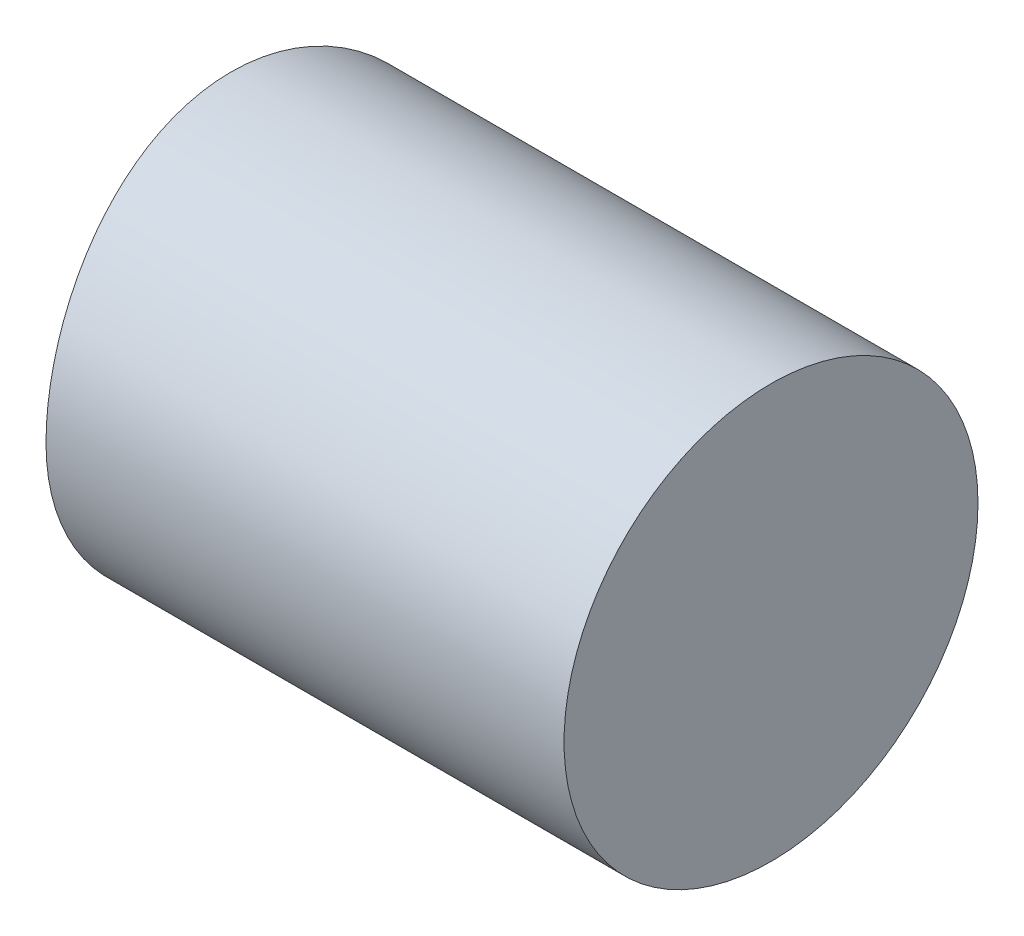
SolidWorks part; units mm, degrees
ref_plane "Front Plane" through (0, 0, 0) normal (0, 0, 1) x (1, 0, 0)
ref_plane "Top Plane" through (0, 0, 0) normal (0, 1, 0) x (1, 0, 0)
ref_plane "Right Plane" through (0, 0, 0) normal (1, 0, 0) x (0, 0, -1)
sketch "Sketch3" plane through (0, 0, 0) normal (1, 0, 0) x (0, 0, -1)
  circle A0 centre (0, 0) radius 2.921
  dimension "D1" = 5.842
extrude "Boss-Extrude2" add sketch "Sketch3" along normal blind 7.62
sketch "Sketch4" plane through (0, 0, 0) normal (0, 0, 1) x (1, 0, 0)
  line L0 (0.3088, 0) -> (0.3088, -2.921)
  line L1 (0, -2.921) -> (7.62, -2.921) construction
  line L2 (0.3088, -2.921) -> (0, -2.921)
  line L3 (0, -2.921) -> (0, 2.921)
  arc A0 (0.3088, 0) -> (0, 2.921) centre (-13.6612, 0) ccw
  dimension "D1" = 13.97
extrude "Cut-Extrude1" cut sketch "Sketch4" against normal up to surface and the other way up to surface up to face at (7.62, 0, -2.921) other way up to face at (7.62, 0, -2.921)
sketch "Sketch5" plane through (0, 0, 0) normal (0, 1, 0) x (1, 0, 0)
  line L0 (7.62, 2.921) -> (0.3088, 2.921) construction
  line L1 (2.8488, 2.921) -> (4.3728, 2.921)
  line L2 (2.8488, 2.921) -> (2.8488, 2.159)
  line L3 (2.8488, 2.159) -> (4.3728, 2.159)
  line L4 (4.3728, 2.921) -> (4.3728, 2.159)
  dimension "D1" = 2.54
  dimension "D2" = 1.524
  dimension "D3" = 0.762
extrude "Cut-Extrude2" cut sketch "Sketch5" against normal up to surface and the other way up to surface up to face at (7.62, 0, -2.921) other way up to face at (7.62, 0, -2.921)
